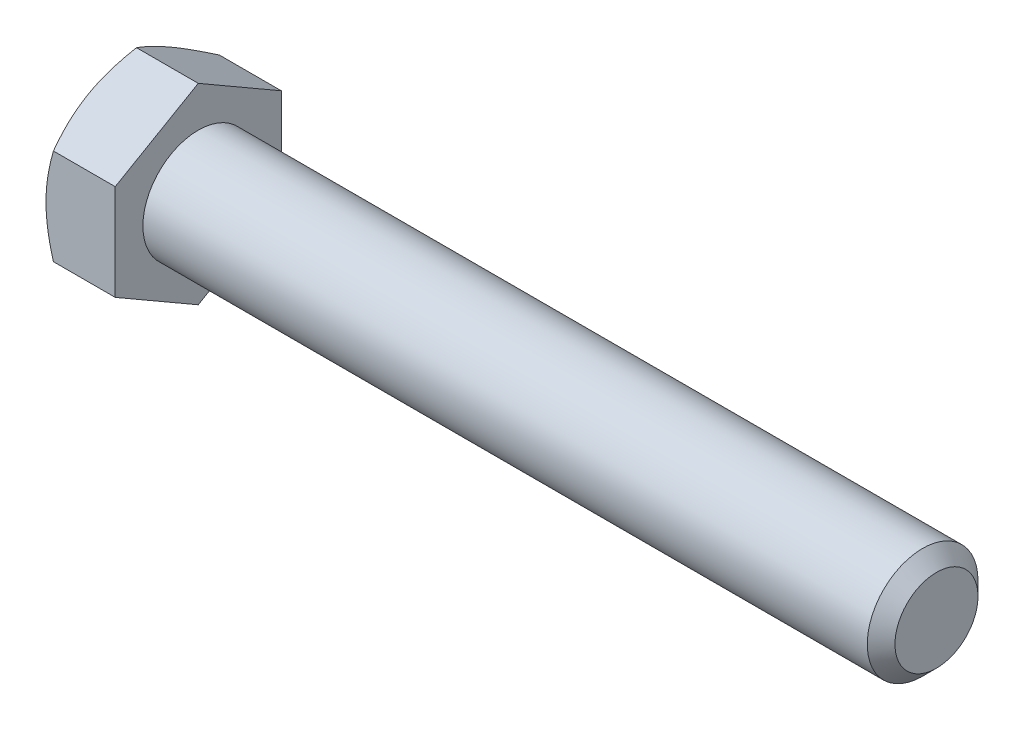
SolidWorks part; units mm, degrees
ref_plane "Front Plane" through (0, 0, 0) normal (0, 0, 1) x (1, 0, 0)
ref_plane "Top Plane" through (0, 0, 0) normal (0, 1, 0) x (1, 0, 0)
ref_plane "Right Plane" through (0, 0, 0) normal (1, 0, 0) x (0, 0, -1)
sketch "Sketch1" plane through (0, 0, 0) normal (0, 0, 1) x (1, 0, 0)
  line L0 (-34.7266, 0) -> (34.7266, 0) construction
  line L1 (34.7266, 4.7625) -> (34.7266, -4.7625) construction
  line L2 (-28.7734, 7.1438) -> (-28.7734, -7.1438) construction
  line L3 (-34.7266, 7.1437) -> (-34.7266, -7.1437) construction
  point P9 (-28.7734, 0)
  point P10 (29.1703, -4.7625)
  dimension "Screw Dia" = 9.525
  dimension "Hex" = 14.2875
  dimension "Head Ht" = 5.9531
  dimension "Screw Lenght" = 63.5
  dimension "D1" = 5.5562
ref_plane "Plane2" through (34.7266, 0, 0) normal (1, 0, 0) x (0, 0, -1)
sketch "Sketch5" plane through (34.7266, 0, 0) normal (1, 0, 0) x (0, 0, -1)
  circle A0 centre (0, 0) radius 4.7625
extrude "Boss-Extrude3" add sketch "Sketch5" against normal up to vertex (63.5 mm away) up to point (-28.7734, 0, 0)
sketch "Sketch9" plane through (34.7266, 0, 0) normal (1, 0, 0) x (0, 0, -1)
  circle A1 centre (0, 0) radius 4.7625
  circle A2 centre (0, 0) radius 4.7625
  dimension "D1" = 0
curve "Helix/Spiral1" pitch 1.5875 height 65.0875 turns 41 parameters "Pitch"=1.5875
chamfer "Chamfer1" distance 1.1906 angle 45 1 edges at (34.7266, 0, -4.7625)
sketch "Sketch10" plane through (0, 0, 0) normal (0, 0, 1) x (1, 0, 0)
  line L0 (34.7266, 4.7625) -> (35.3219, 3.7314)
  line L1 (35.3219, 3.7314) -> (35.5203, 3.7314)
  line L2 (35.5203, 3.7314) -> (36.1156, 4.7625)
  line L3 (34.7266, 4.7625) -> (36.1156, 4.7625)
  line L4 (35.4211, 4.7625) -> (35.4211, 3.7314) construction
  line L5 (35.0242, 4.2469) -> (35.818, 4.2469) construction
  dimension "D1" = 60
  dimension "D2" = 0.1984
  dimension "D3" = 0.7937
sketch "Sketch6" plane through (-28.7734, 0, 0) normal (-1, 0, 0) x (0, 0, 1)
  line L0 (0, 7.1438) -> (0, -7.1438) construction
  line L1 (7.1437, 4.1244) -> (0, 8.2489)
  line L2 (0, 8.2489) -> (-7.1438, 4.1244)
  line L3 (-7.1438, 4.1244) -> (-7.1437, -4.1244)
  line L4 (-7.1437, -4.1244) -> (0, -8.2489)
  line L5 (0, -8.2489) -> (7.1438, -4.1244)
  line L6 (7.1438, -4.1244) -> (7.1437, 4.1244)
  circle A0 centre (0, 0) radius 7.1438 construction
extrude "Boss-Extrude4" add sketch "Sketch6" along normal up to vertex (5.9531 mm away) up to point (-34.7266, -7.1437, 0)
sketch "Sketch7" plane through (-34.7266, 0, 0) normal (-1, 0, 0) x (0, 0, 1)
  circle A0 centre (0, 0) radius 7.1438 construction
  circle A1 centre (0, 0) radius 7.1438
sketch "Sketch8" plane through (-34.7266, 0, 0) normal (-1, 0, 0) x (0, 0, 1)
  circle A0 centre (0, 0) radius 7.1438 construction
  circle A1 centre (0, 0) radius 7.1438
extrude "Cut-Extrude3" cut sketch "Sketch8" against normal through all draft 60 flip side to cut
equation "\"D2@Sketch10\" = \"Pitch@Helix/Spiral1\"*.125"
equation "\"D3@Sketch10\" = \"Pitch@Helix/Spiral1\"*.5"
equation "\"D3@Helix/Spiral1\" = \"Screw Lenght@Sketch1\"+\"Pitch@Helix/Spiral1\""
equation "\"D1@Chamfer1\" = \"Pitch@Helix/Spiral1\"*.75"
equation "\"D1@Sketch1\" = \"Pitch@Helix/Spiral1\"*3.5"
